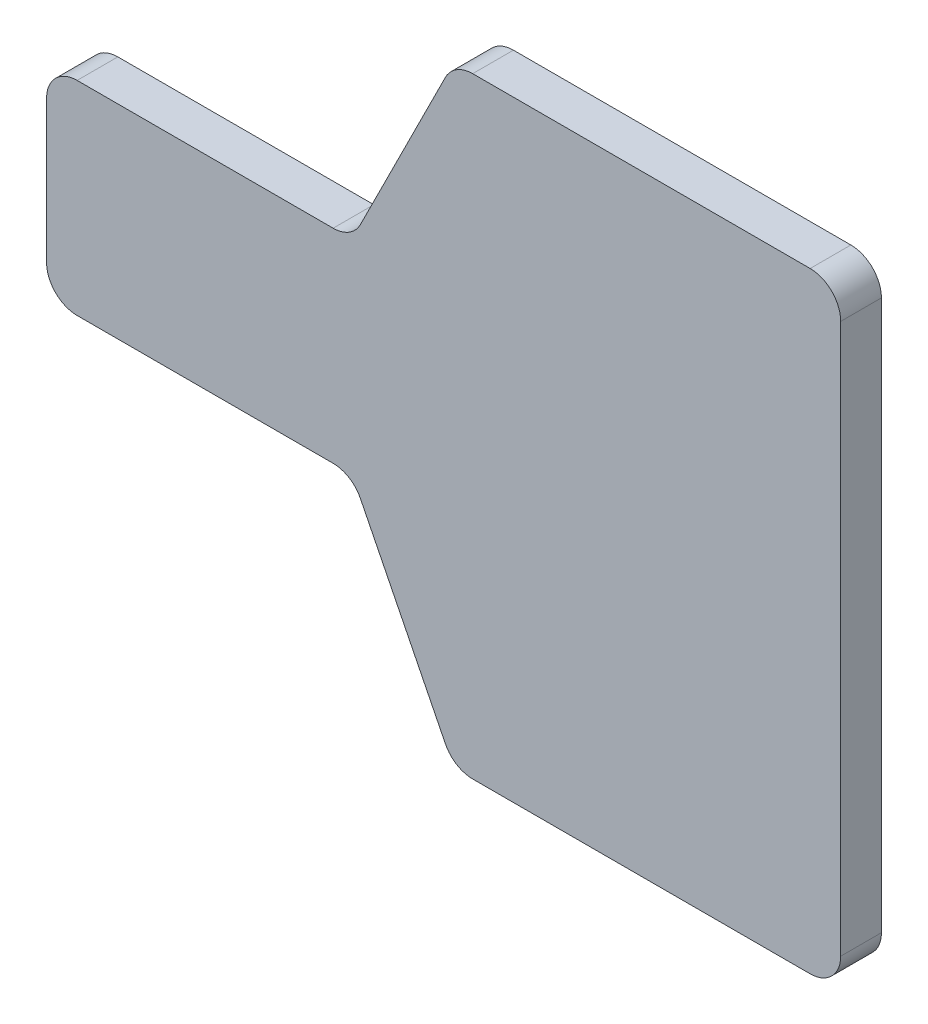
SolidWorks part; units mm, degrees
ref_plane "Front Plane" through (0, 0, 0) normal (0, 0, 1) x (1, 0, 0)
ref_plane "Top Plane" through (0, 0, 0) normal (0, 1, 0) x (1, 0, 0)
ref_plane "Right Plane" through (0, 0, 0) normal (1, 0, 0) x (0, 0, -1)
sketch "Sketch1" plane through (0, 0, 0) normal (0, 0, 1) x (1, 0, 0)
  line L2 (-30, -10) -> (-30, 10)
  line L5 (-30, -10) -> (30, 10) construction
  line L6 (-30, 10) -> (30, -10) construction
  line L7 (30, -30) -> (10, -30)
  line L8 (0, -10) -> (10, -30)
  line L9 (0, -10) -> (-30, -10)
  line L11 (30, 30) -> (10, 30)
  line L12 (10, 30) -> (0, 10)
  line L13 (0, 10) -> (-30, 10)
  line L14 (30, 30) -> (48, 30)
  line L15 (48, 30) -> (48, -30)
  line L16 (48, -30) -> (30, -30)
  point P0 (0, 0)
  dimension "D1" = 20
  dimension "D3" = 38
  dimension "D4" = 20
extrude "Boss-Extrude2" add sketch "Sketch1" along normal blind 4
fillet "Fillet7" radius 3 8 edges at (-30, 10, 2) (0, 10, 2) (10, 30, 2) (48, 30, 2) (48, -30, 2) (10, -30, 2) (0, -10, 2) (-30, -10, 2)
